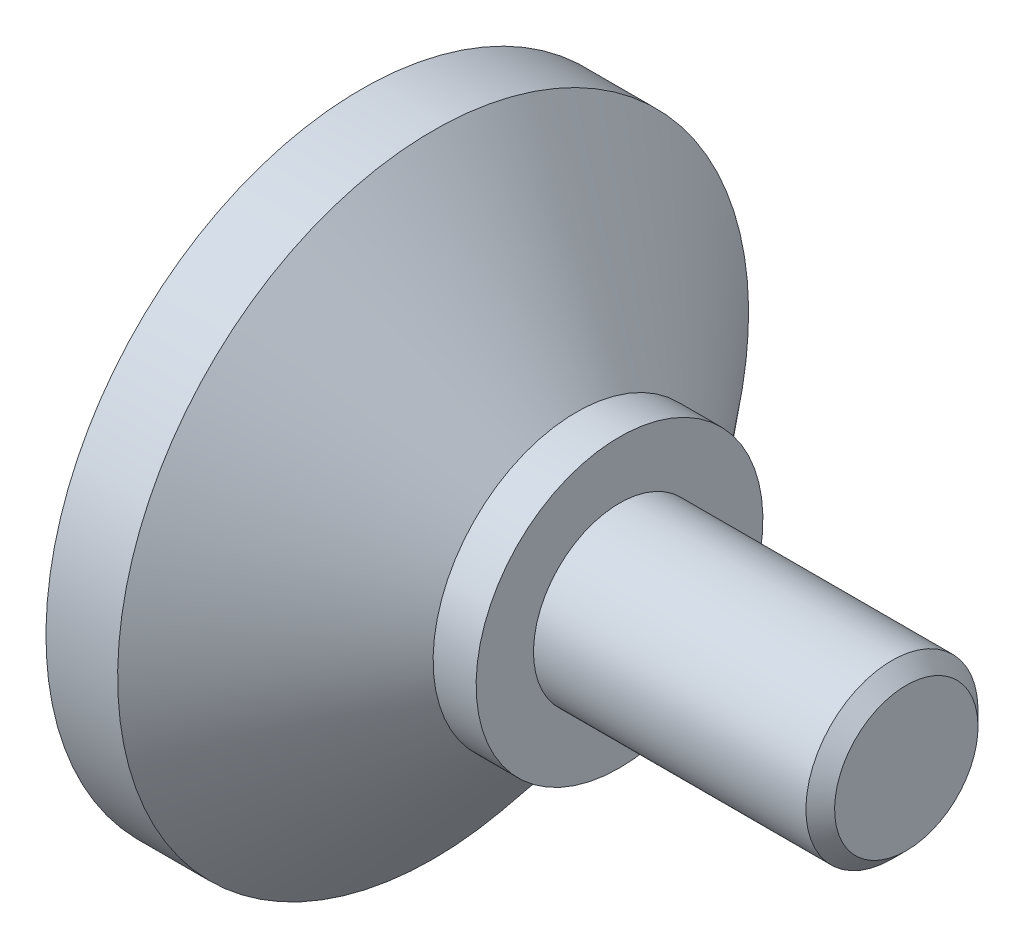
SolidWorks part; units mm, degrees
material "Plain Carbon Steel"
ref_plane "Front Plane" through (0, 0, 0) normal (0, 0, 1) x (1, 0, 0)
ref_plane "Top Plane" through (0, 0, 0) normal (0, 1, 0) x (1, 0, 0)
ref_plane "Right Plane" through (0, 0, 0) normal (1, 0, 0) x (0, 0, -1)
sketch "Sketch1" plane through (0, 0, 0) normal (0, 0, 1) x (1, 0, 0)
  line L0 (-19, 0) -> (19, 0) construction
  line L1 (0, 0) -> (0, 3)
  line L2 (0, 3) -> (-10, 3)
  line L3 (-10, 3) -> (-10, 5)
  line L4 (-10, 5) -> (-11.5, 5)
  line L5 (-11.5, 5) -> (-16.5, 11)
  line L6 (-16.5, 11) -> (-19, 11)
  line L7 (-19, 11) -> (-19, 0)
  line L8 (-19, 0) -> (0, 0)
  point P3 (0, 0)
  dimension "D1" = 10
  dimension "D2" = 9
  dimension "D3" = 7.5
  dimension "D4" = 2.5
  dimension "D5" = 11
  dimension "D6" = 3
  dimension "D7" = 5
revolve "Revolve1" add sketch "Sketch1" angle 360 about L0
chamfer "Chamfer1" distance 0.5 angle 45 1 edges at (0, -3, 0)
